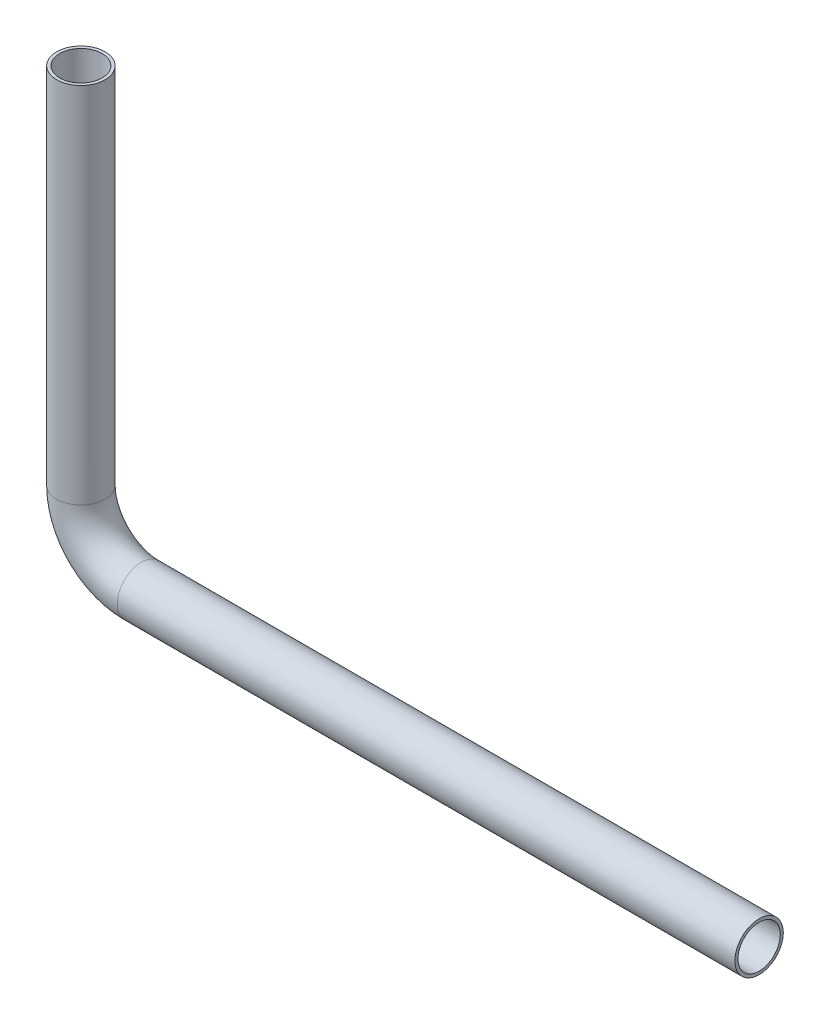
SolidWorks part; units mm, degrees
ref_plane "Front Plane" through (0, 0, 0) normal (0, 0, 1) x (1, 0, 0)
ref_plane "Top Plane" through (0, 0, 0) normal (0, 1, 0) x (1, 0, 0)
ref_plane "Right Plane" through (0, 0, 0) normal (1, 0, 0) x (0, 0, -1)
sketch "Sketch1" plane through (0, 0, 0) normal (0, 0, 1) x (1, 0, 0)
  line L0 (-102, 0) -> (0, 0)
  line L1 (-112, 10) -> (-112, 70)
  arc A0 (-102, 0) -> (-112, 10) centre (-102, 10) cw
  point P5 (0, 0)
  point P7 (-10, 90)
  point P8 (-10, 90)
  point P9 (-4.0594, 80.861)
  point P10 (0, 0)
  point P11 (0, 0)
  point P12 (0, 0)
  point P13 (0, 0)
  dimension "D3" = 10
  dimension "D1" = 112
  dimension "D2" = 60
sweep "Sweep1" add path "Sketch1" circular profile diameter 8 parameters "D3"=8
shell "Shell1" thickness 0.5
